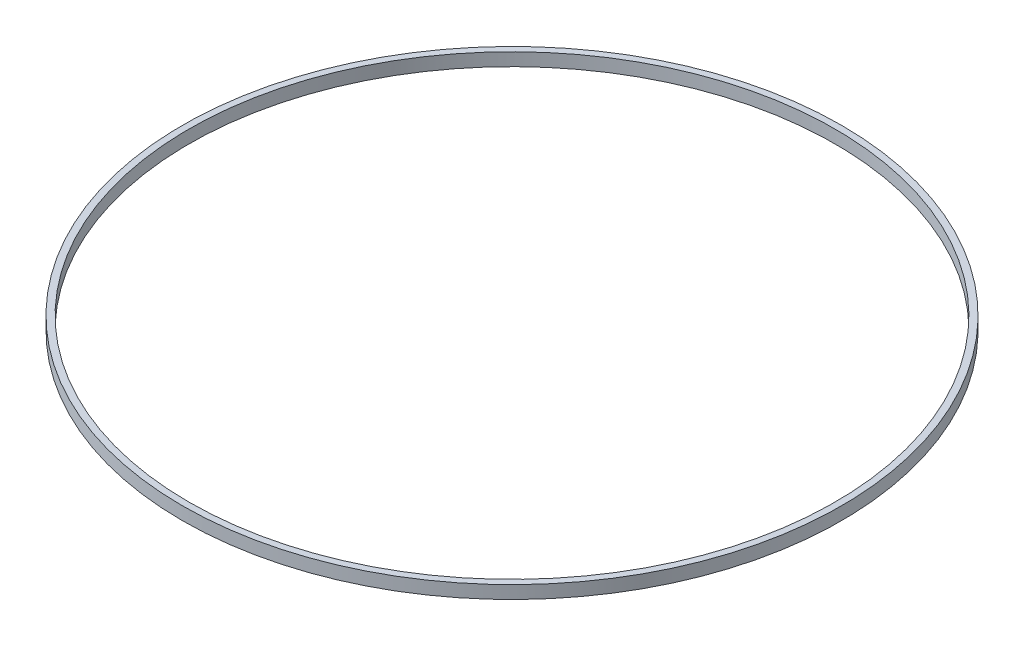
SolidWorks part; units mm, degrees
ref_plane "Front Plane" through (0, 0, 0) normal (0, 0, 1) x (1, 0, 0)
ref_plane "Top Plane" through (0, 0, 0) normal (0, 1, 0) x (1, 0, 0)
ref_plane "Right Plane" through (0, 0, 0) normal (1, 0, 0) x (0, 0, -1)
sketch "Sketch1" plane through (0, 0, 0) normal (0, 1, 0) x (1, 0, 0)
  circle A0 centre (0, 0) radius 51
  circle A1 centre (0, 0) radius 50
  dimension "D1" = 102
  dimension "D2" = 100
extrude "Boss-Extrude1" add sketch "Sketch1" along normal blind 2
